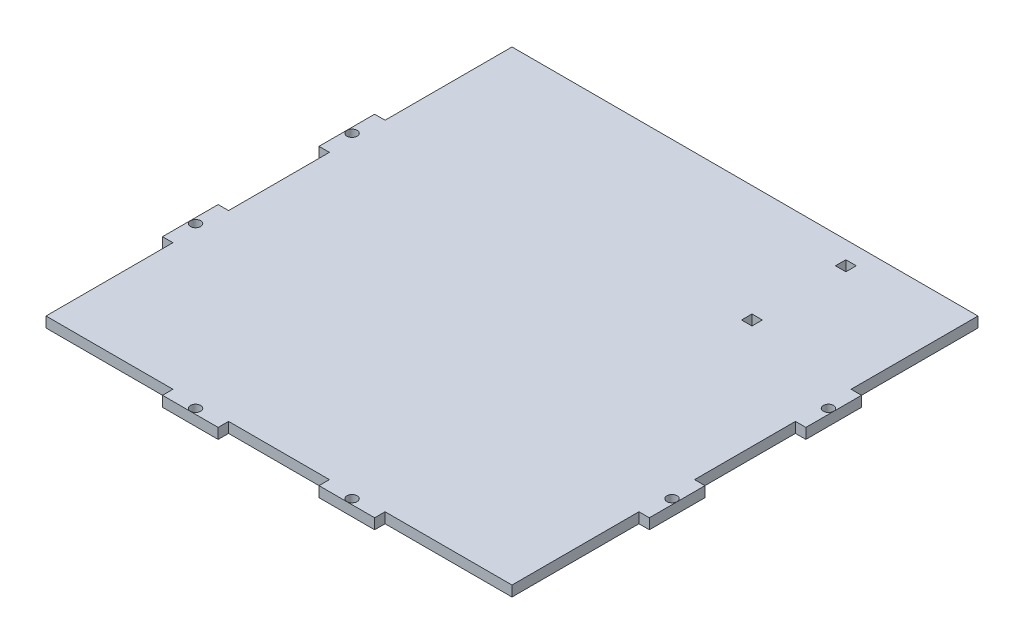
SolidWorks part; units mm, degrees
ref_plane "Front Plane" through (0, 0, 0) normal (0, 0, 1) x (1, 0, 0)
ref_plane "Top Plane" through (0, 0, 0) normal (0, 1, 0) x (1, 0, 0)
ref_plane "Right Plane" through (0, 0, 0) normal (1, 0, 0) x (0, 0, -1)
sketch "Sketch1" plane through (0, 0, 0) normal (0, 1, 0) x (1, 0, 0)
  line L0 (-70, 70) -> (70, -70)
  line L1 (-70, 70) -> (70, 70)
  line L2 (-70, 70) -> (-70, -70)
  line L3 (-70, -70) -> (70, -70)
  line L4 (70, 70) -> (70, -70)
  line L5 (-70, -70) -> (70, 70)
  point P4 (0, 0)
  dimension "D1" = 140
  dimension "D2" = 140
extrude "Boss-Extrude1" add sketch "Sketch1" along normal blind 3 contours L0 L5 L1 | L2 L5 L0 | L5 L3 L0 | L5 L0 L4
sketch "Sketch2" plane through (0, 3, 0) normal (0, 1, 0) x (1, 0, 0)
  line L0 (-70, 70) -> (-70, 67)
  line L1 (-70, 70) -> (-70, -70) construction
  line L2 (-70, 67) -> (-30.5, 67)
  line L3 (-30.5, 67) -> (-30.5, 70)
  line L4 (-70, 70) -> (70, 70) construction
  line L5 (-30.5, 70) -> (-70, 70)
  line L6 (0, -1.65) -> (0, 1.65) construction
  line L7 (30.5, 67) -> (30.5, 70)
  line L8 (70, 67) -> (30.5, 67)
  line L9 (70, 70) -> (70, 67)
  line L10 (30.5, 70) -> (70, 70)
  line L11 (-1.65, 0) -> (1.65, 0) construction
  line L12 (70, -67) -> (30.5, -67)
  line L13 (70, -70) -> (70, -67)
  line L14 (30.5, -70) -> (70, -70)
  line L15 (30.5, -67) -> (30.5, -70)
  line L16 (-30.5, -67) -> (-30.5, -70)
  line L17 (-70, -67) -> (-30.5, -67)
  line L18 (-70, -70) -> (-70, -67)
  line L19 (-30.5, -70) -> (-70, -70)
  line L20 (-67, 30.5) -> (-67, 70)
  line L21 (-67, 70) -> (-70, 70)
  line L22 (-70, 70) -> (-70, 30.5)
  line L23 (-70, 30.5) -> (-67, 30.5)
  line L24 (67, 70) -> (70, 70)
  line L25 (67, 30.5) -> (67, 70)
  line L26 (70, 30.5) -> (67, 30.5)
  line L27 (70, 70) -> (70, 30.5)
  line L28 (67, -70) -> (70, -70)
  line L29 (67, -30.5) -> (67, -70)
  line L30 (70, -30.5) -> (67, -30.5)
  line L31 (70, -70) -> (70, -30.5)
  line L32 (-67, -70) -> (-70, -70)
  line L33 (-67, -30.5) -> (-67, -70)
  line L34 (-70, -30.5) -> (-67, -30.5)
  line L35 (-70, -70) -> (-70, -30.5)
  line L36 (-14.5, 70) -> (-14.5, 67)
  line L37 (-14.5, 67) -> (14.5, 67)
  line L38 (14.5, 67) -> (14.5, 70)
  line L39 (14.5, 70) -> (-14.5, 70)
  line L40 (14.5, -67) -> (14.5, -70)
  line L41 (-14.5, -67) -> (14.5, -67)
  line L42 (-14.5, -70) -> (-14.5, -67)
  line L43 (14.5, -70) -> (-14.5, -70)
  line L44 (70, -14.5) -> (70, 14.5)
  line L45 (-70, 14.5) -> (-67, 14.5)
  line L46 (-67, 14.5) -> (-67, -14.5)
  line L47 (-67, -14.5) -> (-70, -14.5)
  line L48 (-70, -14.5) -> (-70, 14.5)
  line L49 (67, -14.5) -> (70, -14.5)
  line L50 (67, 14.5) -> (67, -14.5)
  line L51 (70, 14.5) -> (67, 14.5)
  dimension "D1" = 39.5
  dimension "D2" = 3
  dimension "D3" = 3
  dimension "D4" = 39.5
  dimension "D5" = 29
  dimension "D6" = 55.5
  dimension "D7" = 29
  dimension "D8" = 55.5
  dimension "D9" = 3
extrude "Cut-Extrude2" cut sketch "Sketch2" against normal blind 3 contours L0 L2 L3 L5 | L22 L23 L20 L21 | L48 L45 L46 L47 | L35 L34 L33 L32 | L18 L17 L16 L19 | L41 L40 L43 L42 | L13 L12 L15 L14 | L31 L30 L29 L28 | L50 L49 L44 L51 | L27 L26 L25 L24 | L9 L8 L7 L10 | L39 L36 L37 L38
sketch "Sketch3" plane through (0, 3, 0) normal (0, 1, 0) x (1, 0, 0)
  line L0 (30.5, -68.5) -> (14.5, -68.5) construction
  line L1 (30.5, -67) -> (30.5, -70) construction
  line L2 (14.5, -67) -> (14.5, -70) construction
  line L3 (0, -1.65) -> (0, 1.65) construction
  line L4 (-1.65, 0) -> (1.65, 0) construction
  line L5 (68.5, -30.5) -> (68.5, -14.5) construction
  line L6 (70, -30.5) -> (67, -30.5) construction
  line L7 (67, -14.5) -> (70, -14.5) construction
  circle A0 centre (22.5, -68.5) radius 1.47
  circle A1 centre (-22.5, -68.5) radius 1.47
  circle A2 centre (-22.5, 68.5) radius 1.47
  circle A3 centre (22.5, 68.5) radius 1.47
  circle A4 centre (68.5, -22.5) radius 1.47
  circle A5 centre (-68.5, -22.5) radius 1.47
  circle A6 centre (-68.5, 22.5) radius 1.47
  circle A7 centre (68.5, 22.5) radius 1.47
  dimension "D1" = 2.94
  dimension "D2" = 2.94
extrude "Cut-Extrude3" cut sketch "Sketch3" against normal blind 3
sketch "Sketch4" plane through (0, 3, 0) normal (0, 1, 0) x (1, 0, 0)
  line L1 (30.5, 70) -> (14.5, 70)
  line L2 (30.5, 70) -> (30.5, 67)
  line L3 (30.5, 67) -> (14.5, 67)
  line L4 (14.5, 70) -> (14.5, 67)
extrude "Cut-Extrude6" cut sketch "Sketch4" against normal blind 3
sketch "Sketch6" plane through (0, 3, 0) normal (0, 1, 0) x (1, 0, 0)
  line L1 (-14.5, 70) -> (-30.5, 70)
  line L2 (-14.5, 70) -> (-14.5, 67)
  line L3 (-14.5, 67) -> (-30.5, 67)
  line L4 (-30.5, 70) -> (-30.5, 67)
extrude "Cut-Extrude7" cut sketch "Sketch6" against normal blind 3
sketch "Sketch7" plane through (0, 3, 0) normal (0, 1, 0) x (1, 0, 0)
  line L0 (67, 30.5) -> (67, 67) construction
  line L1 (37, 32) -> (34, 32)
  line L2 (37, 32) -> (37, 35)
  line L3 (37, 35) -> (34, 35)
  line L4 (34, 32) -> (34, 35)
  line L5 (34, 62) -> (37, 62)
  line L6 (34, 62) -> (34, 59)
  line L7 (34, 59) -> (37, 59)
  line L8 (37, 62) -> (37, 59)
  line L9 (-67, 67) -> (67, 67) construction
  dimension "D1" = 3
  dimension "D2" = 30
  dimension "D3" = 5
  dimension "D4" = 30
extrude "Cut-Extrude8" cut sketch "Sketch7" against normal blind 3
